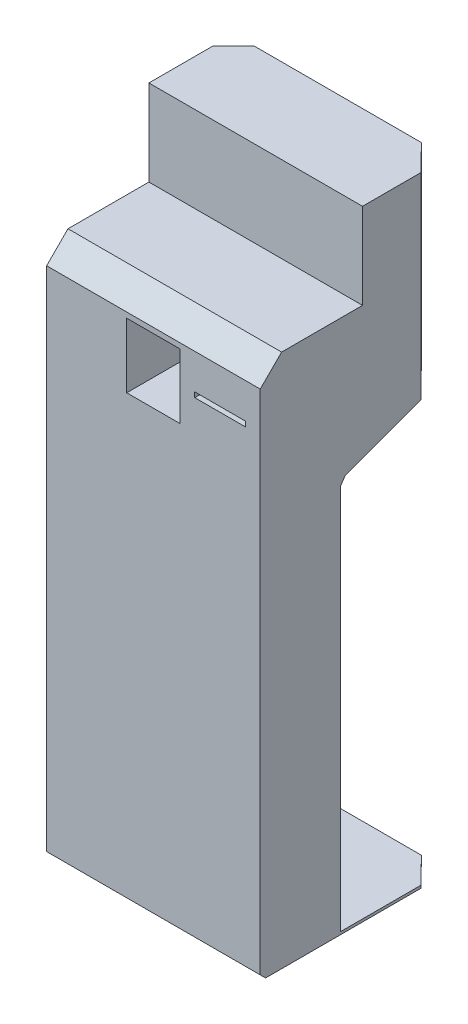
SolidWorks part; units mm, degrees
ref_plane "Front Plane" through (0, 0, 0) normal (0, 0, 1) x (1, 0, 0)
ref_plane "Top Plane" through (0, 0, 0) normal (0, 1, 0) x (1, 0, 0)
ref_plane "Right Plane" through (0, 0, 0) normal (1, 0, 0) x (0, 0, -1)
sketch "Sketch1" plane through (0, 0, 0) normal (1, 0, 0) x (0, 0, -1)
  line L0 (0, 0) -> (-340, 0)
  line L1 (-350, 10) -> (-350, 960)
  line L2 (-310, 1000) -> (-158.4889, 1000)
  line L3 (-158.4889, 1000) -> (-158.4889, 1160.6969)
  line L4 (0, 970) -> (0, 820)
  line L5 (-158.4889, 1160.6969) -> (-350, 1000) construction
  line L6 (-158.4889, 1160.6969) -> (-108.4889, 1160.6969)
  line L7 (-108.4889, 1160.6969) -> (-16.7861, 1024.8641) construction
  line L8 (-310, 1000) -> (-350, 960)
  line L9 (-27.4748, 800) -> (-180, 800) construction
  line L10 (-200, 780) -> (-200, 20) construction
  line L11 (-190, 10) -> (0, 10) construction
  line L12 (0, 10) -> (0, 0) construction
  line L13 (-200, 20) -> (-190, 10) construction
  line L14 (-340, 0) -> (-350, 10)
  line L15 (-180, 800) -> (-200, 780) construction
  line L16 (-9.3969, 806.5798) -> (-27.4748, 800)
  line L17 (-27.4748, 800) -> (-190.6031, 740.6262)
  line L18 (-200, 727.206) -> (-200, 5)
  line L19 (0, 1000) -> (0, 1160.6969)
  line L20 (0, 1160.6969) -> (-108.4889, 1160.6969)
  line L21 (-16.7861, 1024.8641) -> (0, 970) construction
  line L22 (0, 820) -> (-9.3969, 806.5798)
  line L23 (-190.6031, 740.6262) -> (-200, 727.206)
  line L24 (0, 1000) -> (0, 970)
  line L25 (0, 10) -> (-200, 70) construction
  line L26 (-200, 5) -> (0, 5)
  line L27 (0, 5) -> (0, 0)
  arc A0 (0, 1000) -> (-158.4889, 1160.6969) centre (-160.7123, 1000) ccw construction
  arc A1 (-350, 960) -> (-310, 1000) centre (-310, 960) cw construction
  point P1 (-350, 0)
  point P12 (0, 800)
  point P13 (-200, 800)
  point P15 (-200, 10)
  point P23 (0, 810)
  point P25 (-200, 737.206)
  dimension "D5" = 40
  dimension "D1" = 1000
  dimension "D2" = 350
  dimension "D3" = 250
  dimension "D4" = 40
  dimension "D6" = 50
  dimension "D7" = 150
  dimension "D8" = 10
  dimension "D10" = 110
  dimension "D9" = 200
  dimension "D15" = 60
  dimension "D16" = 5
extrude "Boss-Extrude1" add sketch "Sketch1" along normal blind 400
sketch "Sketch2" plane through (0, 0, 350) normal (0, 0, 1) x (1, 0, 0)
  line L0 (200, 950) -> (200, 1000) construction
  line L1 (150, 950) -> (250, 950)
  line L2 (150, 950) -> (150, 829)
  line L3 (150, 829) -> (250, 829)
  line L4 (250, 950) -> (250, 829)
  line L5 (400, 1000) -> (0, 1000) construction
  line L6 (277.35, 889.5) -> (250, 889.5) construction
  line L7 (372.65, 894.2) -> (277.35, 894.2)
  line L8 (372.65, 894.2) -> (372.65, 884.8)
  line L9 (372.65, 884.8) -> (277.35, 884.8)
  line L10 (277.35, 894.2) -> (277.35, 884.8)
  line L11 (250, 950) -> (400, 950) construction
  line L12 (400, 960) -> (400, 10) construction
  line L13 (325, 950) -> (325, 894.2) construction
  dimension "D1" = 121
  dimension "D2" = 100
  dimension "D3" = 50
  dimension "D4" = 9.4
  dimension "D5" = 95.3
extrude "Cut-Extrude1" cut sketch "Sketch2" against normal blind 268
sketch "Sketch3" plane through (0, 0, 0) normal (0, -1, 0) x (-1, 0, 0)
  line L0 (32.9719, -72.8044) -> (-67.7282, 29.5696)
  line L1 (-67.7282, 29.5696) -> (-322.6486, 29.5696)
  line L2 (-322.6486, 29.5696) -> (-423.3487, -72.8044)
  line L3 (-423.3487, -72.8044) -> (-423.3487, 100.0695)
  line L4 (-423.3487, 100.0695) -> (32.9719, 100.0695)
  line L5 (32.9719, 100.0695) -> (32.9719, -72.8044)
  line L6 (-195.1884, 29.5696) -> (-195.1884, -2.4875) construction
  line L8 (-195.1884, 29.5696) -> (-195.1884, 100.0695) construction
extrude "Cut-Extrude2" cut sketch "Sketch3" against normal through all both and the other way through all
